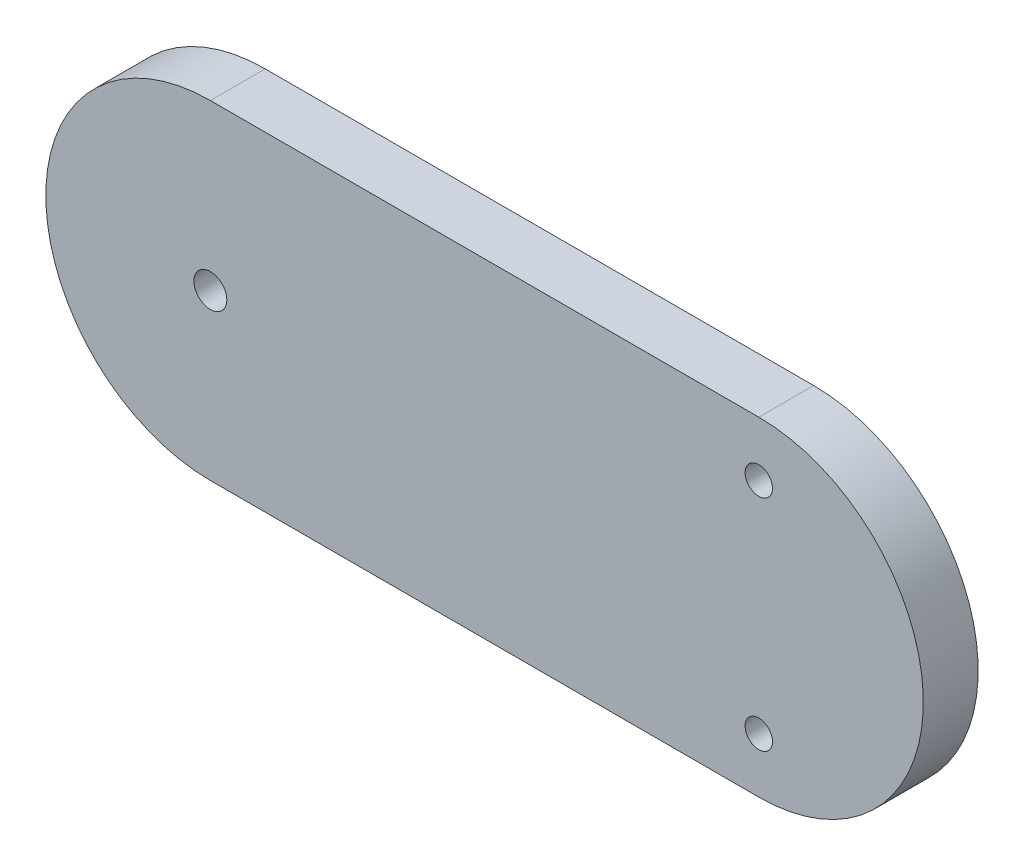
SolidWorks part; units mm, degrees
ref_plane "Front Plane" through (0, 0, 0) normal (0, 0, 1) x (1, 0, 0)
ref_plane "Top Plane" through (0, 0, 0) normal (0, 1, 0) x (1, 0, 0)
ref_plane "Right Plane" through (0, 0, 0) normal (1, 0, 0) x (0, 0, -1)
sketch "Sketch1" plane through (0, 0, 0) normal (0, 0, 1) x (1, 0, 0)
  line L0 (-21.2273, 0) -> (28.7727, 0) construction
  line L1 (-21.2273, 0) -> (28.7727, 0) construction
  line L2 (-21.2273, 15) -> (28.7727, 15)
  line L3 (-21.2273, -15) -> (28.7727, -15)
  line L4 (-21.2273, 8.0624) -> (-21.2273, -9.3012) construction
  line L5 (28.7727, 10) -> (28.7727, -10) construction
  arc A0 (-21.2273, 15) -> (-21.2273, -15) centre (-21.2273, 0) ccw
  arc A1 (28.7727, -15) -> (28.7727, 15) centre (28.7727, 0) ccw
  circle A7 centre (28.7727, -10) radius 1.25
  circle A8 centre (28.7727, 10) radius 1.25
  circle A9 centre (-21.2273, 0) radius 1.5
  point P3 (3.7727, 0)
  dimension "D3" = 2.5
  dimension "D4" = 2.5
  dimension "D5" = 10
  dimension "D7" = 3
  dimension "D1" = 50
  dimension "D2" = 30
  dimension "D6" = 10
extrude "Boss-Extrude1" add sketch "Sketch1" along normal blind 5
